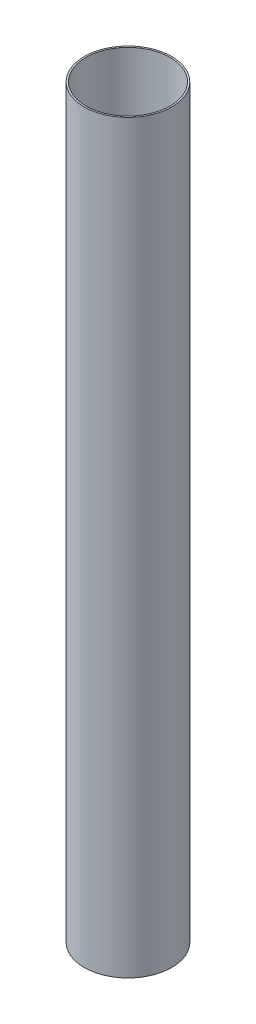
SolidWorks part; units mm, degrees
ref_plane "Front Plane" through (0, 0, 0) normal (0, 0, 1) x (1, 0, 0)
ref_plane "Top Plane" through (0, 0, 0) normal (0, 1, 0) x (1, 0, 0)
ref_plane "Right Plane" through (0, 0, 0) normal (1, 0, 0) x (0, 0, -1)
sketch "Sketch1" plane through (0, 0, 0) normal (0, 1, 0) x (1, 0, 0)
  circle A0 centre (0, 0) radius 27
  dimension "D1" = 54
extrude "Boss-Extrude1" add sketch "Sketch1" along normal blind 460
shell "Shell1" thickness 1
